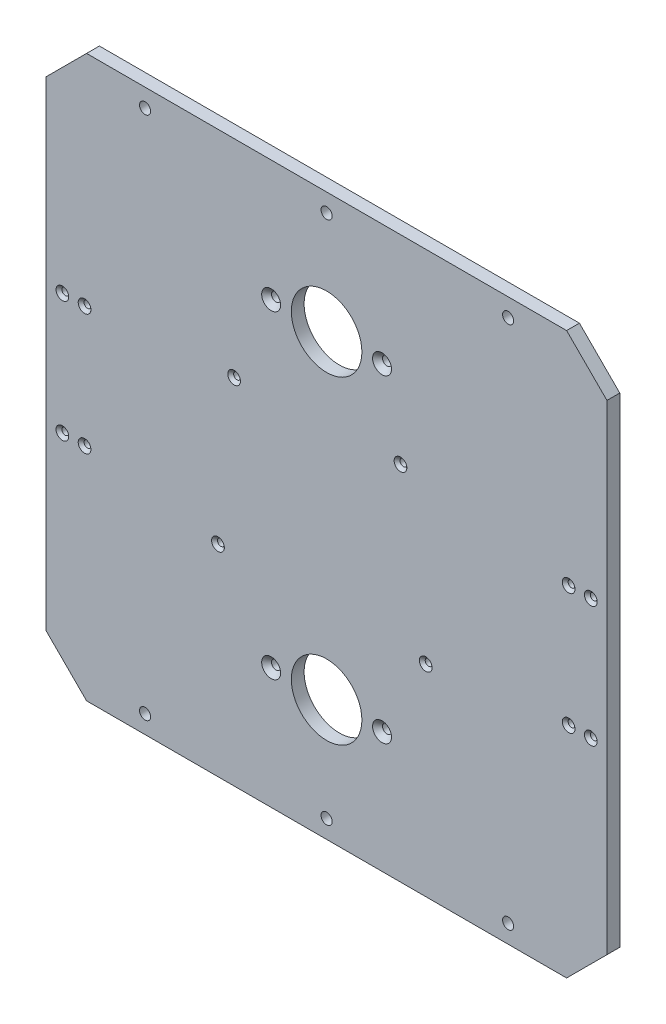
SolidWorks part; units mm, degrees
ref_plane "Front Plane" through (0, 0, 0) normal (0, 0, 1) x (1, 0, 0)
ref_plane "Top Plane" through (0, 0, 0) normal (0, 1, 0) x (1, 0, 0)
ref_plane "Right Plane" through (0, 0, 0) normal (1, 0, 0) x (0, 0, -1)
sketch "Sketch1" plane through (0, 0, 0) normal (0, 0, 1) x (1, 0, 0)
  line L0 (-79.0045, 0) -> (94.053, 0) construction
  line L1 (0, 67.0127) -> (0, -68.6587) construction
  line L3 (139, -139) -> (-139, -139)
  line L4 (139, -139) -> (139, 139)
  line L5 (139, 139) -> (-139, 139)
  line L6 (-139, -139) -> (-139, 139)
  line L7 (139, -139) -> (-139, 139) construction
  line L8 (139, 139) -> (-139, -139) construction
  point P4 (0, 0)
  dimension "D1" = 278
  dimension "D2" = 278
extrude "Boss-Extrude1" add sketch "Sketch1" along normal blind 6.35
chamfer "Chamfer1" distance 20 angle 45 4 edges at (139, -139, 3.175) (139, 139, 3.175) (-139, 139, 3.175) (-139, -139, 3.175)
sketch "Sketch4" plane through (0, 0, 6.35) normal (0, 0, 1) x (1, 0, 0)
  line L0 (0, 186.846) -> (0, -174.5938) construction
  line L1 (219.7737, 0) -> (-232.7917, 0) construction
  line L2 (119, 139) -> (-119, 139) construction
  line L3 (-90, 130) -> (90, 130) construction
  circle A0 centre (-90, 130) radius 2.75
  circle A1 centre (0, 130) radius 2.75
  circle A2 centre (90, 130) radius 2.75
  circle A3 centre (90, -130) radius 2.75
  circle A4 centre (0, -130) radius 2.75
  circle A5 centre (-90, -130) radius 2.75
  dimension "D1" = 5.5
  dimension "D2" = 9
  dimension "D3" = 90
extrude "Cut-Extrude2" cut sketch "Sketch4" against normal blind 76.2
sketch "Sketch8" plane through (0, 0, 6.35) normal (0, 0, 1) x (1, 0, 0)
  line L0 (0, 225.553) -> (0, -227.4564) construction
  line L1 (119, 139) -> (-119, 139) construction
  line L2 (139, 0) -> (-139, 0) construction
  line L3 (139, -119) -> (139, 119) construction
  line L4 (-139, 119) -> (-139, -119) construction
  circle A0 centre (0, 79) radius 17.5
  circle A1 centre (0, -79) radius 17.5
  dimension "D3" = 35
  dimension "D1" = 60
extrude "Cut-Extrude4" cut sketch "Sketch8" against normal blind 105
hole_wizard "CSK for M4 Flat Head Machine Screw2" positions "Sketch10" profile "Sketch9" countersink size "M4" standard "ANSI Metric" end condition through all
sketch "Sketch10" plane through (0, 0, 6.35) normal (0, 0, 1) x (1, 0, 0)
  line L5 (0, 205.0159) -> (0, -212.7914) construction
  line L8 (156.7583, 0) -> (-175.5166, 0) construction
  line L18 (0, 79) -> (17.5, 79) construction
  circle A1 centre (0, 79) radius 17.5 construction
  point P113 (27.5, 79)
  point P117 (-27.5, 79)
  point P119 (-27.5, -79)
  point P120 (27.5, -79)
  dimension "D1" = 55
sketch "Sketch9" plane through (27.5, 79, 6.35) normal (1, 0, 0) x (0, -1, 0)
  line L0 (0, 0) -> (0, 6.35)
  line L1 (0, 6.35) -> (2.25, 6.35)
  line L2 (2.25, 6.35) -> (2.25, 2.45)
  line L3 (2.25, 2.45) -> (4.7, 0)
  line L5 (4.7, 0) -> (0, 0)
  line L6 (-2.25, 2.45) -> (-4.7, 0) construction
  line L11 (0, -6.35) -> (0, 107.95) construction
  dimension "Thru Hole Dia." = 4.5
  dimension "Thru Hole Depth" = 6.35
  dimension "Near C'Sink Dia." = 9.4
  dimension "Near C'Sink Angle" = 90
hole_wizard "CSK for M3 Flat Head Machine Screw1" positions "Sketch12" profile "Sketch11" countersink size "M3" standard "ANSI Metric" end condition through all
sketch "Sketch12" plane through (0, 0, 6.35) normal (0, 0, 1) x (1, 0, 0)
  line L0 (0, 139) -> (0, -139) construction
  line L1 (119, 139) -> (-119, 139) construction
  line L2 (-119, -139) -> (119, -139) construction
  line L4 (-139, 0) -> (139, 0) construction
  line L5 (-139, 119) -> (-139, -119) construction
  line L6 (139, -119) -> (139, 119) construction
  point P0 (-131, 30)
  point P2 (-120, 30)
  point P24 (-120, -30)
  point P25 (-131, -30)
  point P26 (131, -30)
  point P27 (120, -30)
  point P28 (120, 30)
  point P29 (131, 30)
  dimension "D1" = 11
  dimension "D2" = 60
  dimension "D3" = 8
sketch "Sketch11" plane through (-131, 30, 6.35) normal (1, 0, 0) x (0, -1, 0)
  line L0 (0, 0) -> (0, 6.35)
  line L1 (0, 6.35) -> (1.7, 6.35)
  line L2 (1.7, 6.35) -> (1.7, 1.45)
  line L3 (1.7, 1.45) -> (3.15, 0)
  line L5 (3.15, 0) -> (0, 0)
  line L6 (-1.7, 1.45) -> (-3.15, 0) construction
  line L11 (0, -6.35) -> (0, 107.95) construction
  dimension "Thru Hole Dia." = 3.4
  dimension "Thru Hole Depth" = 6.35
  dimension "Near C'Sink Dia." = 6.3
  dimension "Near C'Sink Angle" = 90
sketch "Sketch13" plane through (0, 0, 0) normal (0, 0, 1) x (1, 0, 0)
  point P1 (49.1415, -39.1273)
  point P6 (41.1415, 36.3727)
  point P10 (-41.3585, 40.3727)
  point P14 (-53.8585, -39.1273)
hole_wizard "CSK for M3 Flat Head Machine Screw2" positions "Sketch15" profile "Sketch14" countersink size "M3" standard "ANSI Metric" end condition through all
sketch "Sketch15" plane through (0, 0, 6.35) normal (0, 0, 1) x (1, 0, 0)
  point P0 (-45.8585, 36.3727)
  point P2 (-53.8585, -39.1273)
  point P4 (36.6415, 40.3727)
  point P6 (49.1415, -39.1273)
sketch "Sketch14" plane through (-45.8585, 36.3727, 6.35) normal (1, 0, 0) x (0, -1, 0)
  line L0 (0, 0) -> (0, 6.35)
  line L1 (0, 6.35) -> (1.7, 6.35)
  line L2 (1.7, 6.35) -> (1.7, 1.45)
  line L3 (1.7, 1.45) -> (3.15, 0)
  line L5 (3.15, 0) -> (0, 0)
  line L6 (-1.7, 1.45) -> (-3.15, 0) construction
  line L11 (0, -6.35) -> (0, 107.95) construction
  dimension "Thru Hole Dia." = 3.4
  dimension "Thru Hole Depth" = 6.35
  dimension "Near C'Sink Dia." = 6.3
  dimension "Near C'Sink Angle" = 90
equation "\"plate_thickness\" = 6.35 'thickness of the plate "
equation "\"height\"= 180"
equation "\"D1@Boss-Extrude1\"=\"plate_thickness\""
equation "\"t_height\" = 200"
equation "\"t_width\" = 240"
equation "\"t_length\" = 240"
equation "\"plate_spacing\" = 1"
equation "\"front_plate_height\" = \"t_height\" + 38"
equation "\"front_plate_width\" = \"t_width\" + 38"
equation "\"side_plate_height\" = \"front_plate_height\""
equation "\"side_plate_length\" = \"t_length\" + 38"
equation "\"top_plate_width\" = \"front_plate_width\""
equation "\"top_plate_length\" = \"side_plate_length\""
equation "\"D2@Sketch1\"=\"top_plate_width\""
equation "\"D1@Sketch1\"=\"top_plate_length\""
equation "\"plate_hole_spacing\"= 9"
equation "\"connector_D1\" = 70 'the big holes diameter"
equation "\"connector_mtg_D2\"= 5.5 'mounting holes"
equation "\"mtg_dfc\" = 40 'mounting hole distance from center"
equation "\"mtg_hole_D\" = 5.5 'mounting holes"
equation "\"plate_hole_from_edge\" = 9"
equation "\"D1@Sketch4\"=\"mtg_hole_D\""
equation "\"D2@Sketch4\"=\"plate_hole_from_edge\""
equation "\"itx_support_t_slot_length\" = \"t_width\" + (2 * 20.5)"
equation "\"locomotion_length\" = \"t_length\""
equation "\"locomotion_width\" = \"t_width\""
equation "\"locomotion_height\" = 40"
equation "\"itx_mtg_hole_spacing\" = 40"
equation "\"emg30_bracket_hole_len\" = 60"
equation "\"emg30_bracket_hole_wid\" = 11"
equation "\"D2@Sketch12\"=\"emg30_bracket_hole_len\""
equation "\"D1@Sketch12\"=\"emg30_bracket_hole_wid\""
